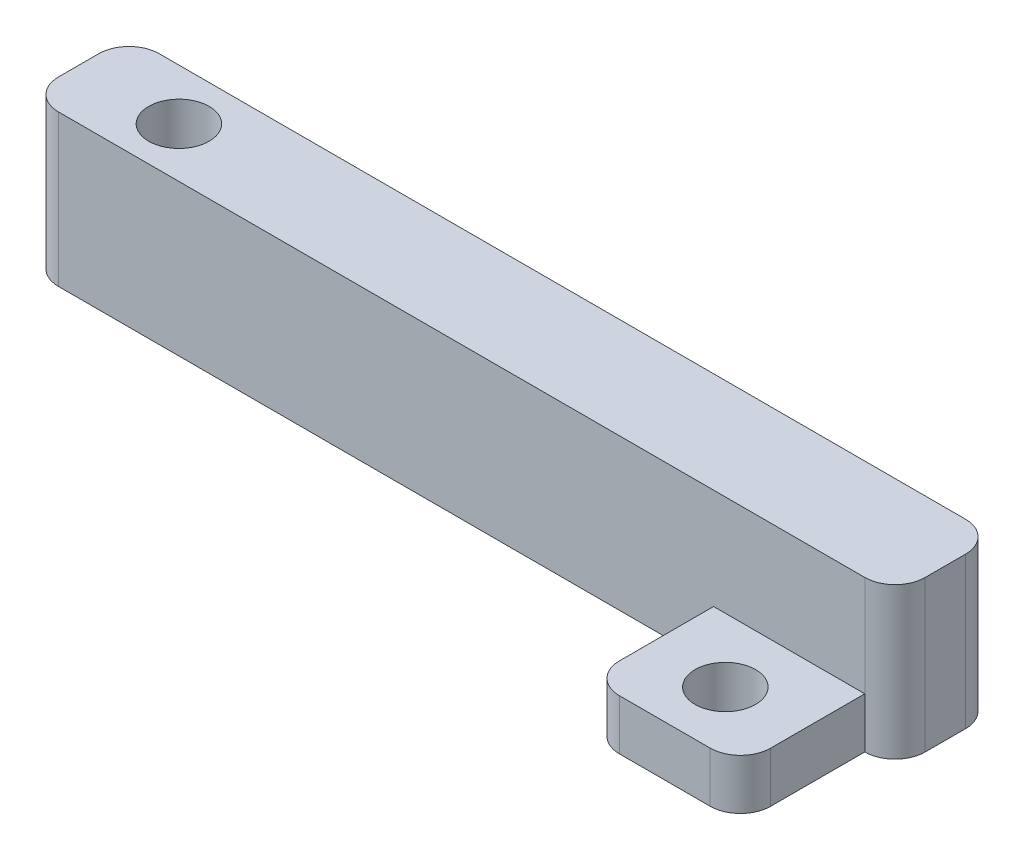
SolidWorks part; units mm, degrees
ref_plane "Front Plane" through (0, 0, 0) normal (0, 0, 1) x (1, 0, 0)
ref_plane "Top Plane" through (0, 0, 0) normal (0, 1, 0) x (1, 0, 0)
ref_plane "Right Plane" through (0, 0, 0) normal (1, 0, 0) x (0, 0, -1)
sketch "Sketch1" plane through (0, 0, 0) normal (0, 1, 0) x (1, 0, 0)
  line L0 (-26.2648, -4.1897) -> (-26.2648, -8.1897)
  line L1 (-23.2648, -11.1897) -> (14.2895, -11.1897)
  line L2 (59.7352, -4.1897) -> (59.7352, -8.1897)
  line L6 (56.7352, -1.1897) -> (-23.2648, -1.1897)
  line L13 (14.2895, -11.1897) -> (56.7352, -11.1897)
  arc A0 (56.7352, -11.1897) -> (59.7352, -8.1897) centre (56.7352, -8.1897) ccw
  arc A1 (56.7352, -1.1897) -> (59.7352, -4.1897) centre (56.7352, -4.1897) cw
  arc A6 (-26.2648, -8.1897) -> (-23.2648, -11.1897) centre (-23.2648, -8.1897) ccw
  arc A7 (-26.2648, -4.1897) -> (-23.2648, -1.1897) centre (-23.2648, -4.1897) cw
  circle A10 centre (-16.2648, -6.238) radius 1.4
  point P28 (-26.2648, -11.1897)
  point P31 (-26.2648, -1.1897)
  point P37 (49.7352, 9.8103)
  dimension "D1" = 3
  dimension "D4" = 80
  dimension "D3" = 10
  dimension "D2" = 10
extrude "Boss-Extrude1" add sketch "Sketch1" along normal blind 15
sketch "Sketch3" plane through (0, 0, 0) normal (0, -1, 0) x (1, 0, 0)
  circle A0 centre (-16.2648, 6.238) radius 3
extrude "Cut-Extrude2" cut sketch "Sketch3" against normal blind 3
sketch "Sketch4" plane through (0, 15, 0) normal (0, 1, 0) x (1, 0, 0)
  circle A0 centre (-16.2648, -6.238) radius 3
extrude "Cut-Extrude3" cut sketch "Sketch4" against normal blind 10
sketch "Sketch5" plane through (0, 0, 0) normal (0, -1, 0) x (1, 0, 0)
  line L1 (56.7352, 11.1897) -> (41.7352, 11.1897)
  line L2 (56.7352, 11.1897) -> (56.7352, 20.524)
  line L3 (53.7352, 23.524) -> (44.7352, 23.524)
  line L4 (41.7352, 11.1897) -> (41.7352, 20.524)
  arc A0 (56.7352, 20.524) -> (53.7352, 23.524) centre (53.7352, 20.524) ccw
  arc A1 (44.7352, 23.524) -> (41.7352, 20.524) centre (44.7352, 20.524) ccw
  point P7 (56.7352, 23.524)
  point P10 (41.7352, 23.524)
  dimension "D2" = 3
  dimension "D1" = 15
extrude "Boss-Extrude2" add sketch "Sketch5" against normal blind 5
sketch "Sketch7" plane through (0, 5, 0) normal (0, 1, 0) x (1, 0, 0)
  line L0 (53.7352, -23.524) -> (44.7352, -23.524) construction
  line L1 (41.7352, -20.524) -> (41.7352, -11.1897) construction
  circle A0 centre (49.2352, -17.524) radius 3
  dimension "D1" = 6
  dimension "D2" = 7.5
extrude "Cut-Extrude4" cut sketch "Sketch7" against normal blind 5
